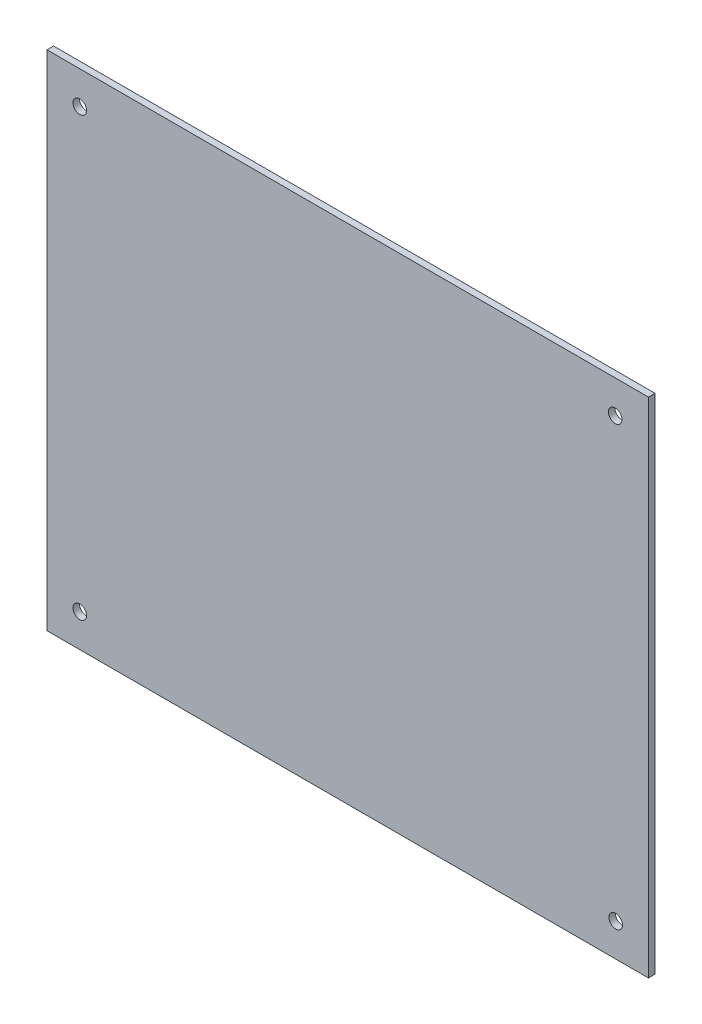
SolidWorks part; units mm, degrees
ref_plane "Alzado" through (0, 0, 0) normal (0, 0, 1) x (1, 0, 0)
ref_plane "Planta" through (0, 0, 0) normal (0, 1, 0) x (1, 0, 0)
ref_plane "Vista lateral" through (0, 0, 0) normal (1, 0, 0) x (0, 0, -1)
sketch "Croquis1" plane through (0, 0, 0) normal (0, 0, 1) x (1, 0, 0)
  line L0 (-122.5, 167.0051) -> (-122.5, -49832.9949) construction
  line L1 (-137.5, 115) -> (137.5, 115)
  line L2 (-137.5, 115) -> (-137.5, -115)
  line L3 (-137.5, -115) -> (137.5, -115)
  line L4 (137.5, 115) -> (137.5, -115)
  line L5 (-137.5, 115) -> (137.5, -115) construction
  line L6 (-137.5, -115) -> (137.5, 115) construction
  line L7 (-173.0544, 100) -> (49826.9456, 100) construction
  line L8 (-226.0645, -100) -> (49773.9355, -100) construction
  line L9 (122.5, 178.733) -> (122.5, -49821.267) construction
  circle A0 centre (-122.5, 100) radius 3.1
  circle A1 centre (122.2752, 100) radius 3.1
  circle A2 centre (-122.5, -100) radius 3.1
  circle A3 centre (122.5, -100) radius 3.1
  point P0 (0, 0)
  dimension "D7" = 6.2
  dimension "D1" = 275
  dimension "D2" = 230
  dimension "D3" = 15
  dimension "D4" = 15
  dimension "D5" = 15
  dimension "D6" = 15
extrude "Saliente-Extruir1" add sketch "Croquis1" along normal blind 3
